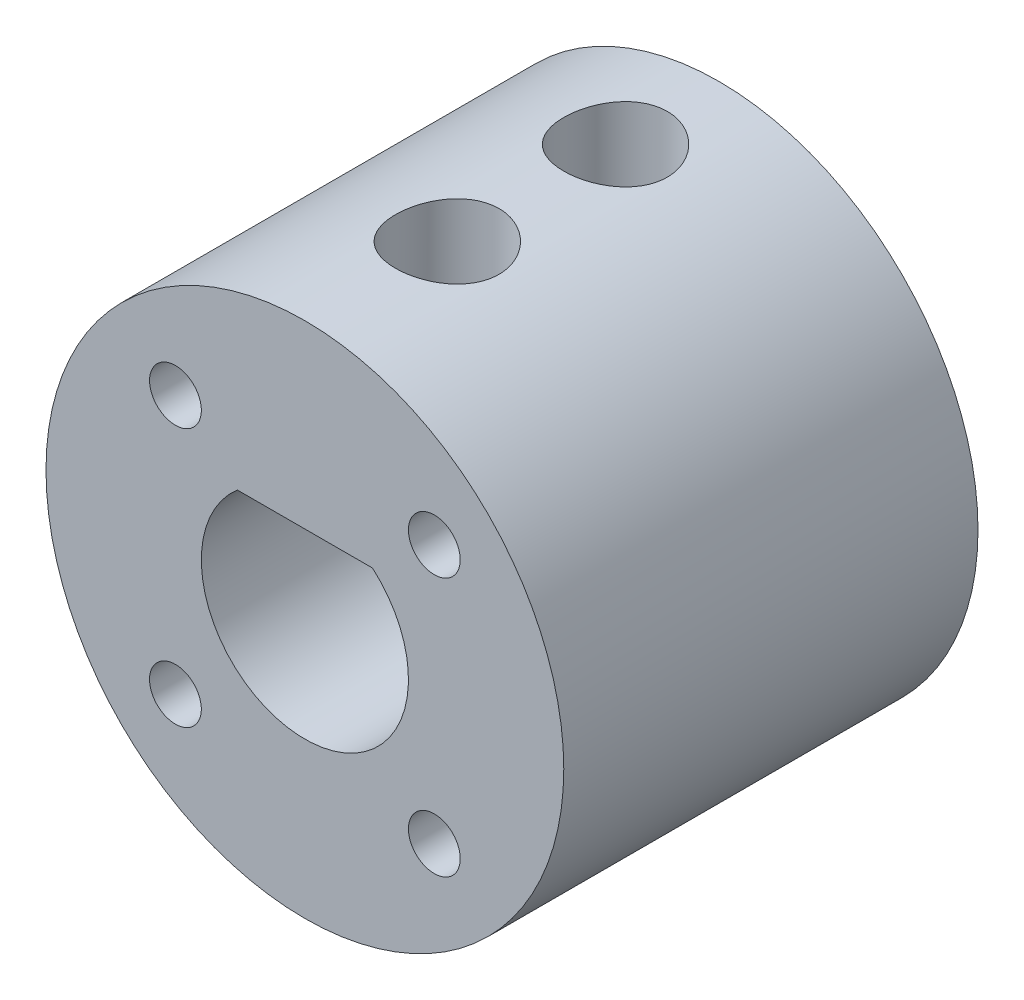
SolidWorks part; units mm, degrees
ref_plane "Alzado" through (0, 0, 0) normal (0, 0, 1) x (1, 0, 0)
ref_plane "Planta" through (0, 0, 0) normal (0, 1, 0) x (1, 0, 0)
ref_plane "Vista lateral" through (0, 0, 0) normal (1, 0, 0) x (0, 0, -1)
sketch "Croquis1" plane through (0, 0, 0) normal (0, 0, 1) x (1, 0, 0)
  line L0 (2.6113, 3.03) -> (-2.6113, 3.03)
  circle A0 centre (0, 0) radius 10
  arc A1 (-2.6113, 3.03) -> (2.6113, 3.03) centre (0, 0) ccw
  dimension "D1" = 8
  dimension "D2" = 20
  dimension "D3" = 3.03
extrude "Saliente-Extruir1" add sketch "Croquis1" along normal blind 16
sketch "Croquis2" plane through (0, 0, 0) normal (0, 1, 0) x (1, 0, 0)
  line L0 (0, 0) -> (0, -14) construction
  circle A0 centre (0, -4) radius 2
  circle A1 centre (0, -10.5) radius 2
  dimension "D2" = 4
  dimension "D1" = 14
  dimension "D3" = 4
  dimension "D4" = 6.5
extrude "Cortar-Extruir1" cut sketch "Croquis2" along normal blind 20
sketch "Croquis3" plane through (0, 0, 0) normal (0, 0, -1) x (-1, 0, 0)
  line L0 (5, -5) -> (-5, 5) construction
  line L1 (-5, -5) -> (5, 5) construction
  line L3 (-3.5, 5) -> (-4.25, 6.299)
  line L4 (-4.25, 6.299) -> (-5.75, 6.299)
  line L5 (-5.75, 6.299) -> (-6.5, 5)
  line L6 (-6.5, 5) -> (-5.75, 3.701)
  line L7 (-5.75, 3.701) -> (-4.25, 3.701)
  line L8 (-4.25, 3.701) -> (-3.5, 5)
  line L9 (6.4995, 5.0386) -> (5.7163, 6.3179)
  line L10 (5.7163, 6.3179) -> (4.2168, 6.2793)
  line L11 (4.2168, 6.2793) -> (3.5005, 4.9614)
  line L12 (3.5005, 4.9614) -> (4.2837, 3.6821)
  line L13 (4.2837, 3.6821) -> (5.7832, 3.7207)
  line L14 (5.7832, 3.7207) -> (6.4995, 5.0386)
  line L15 (6.5, -5.0009) -> (5.7508, -3.7014)
  line L16 (5.7508, -3.7014) -> (4.2508, -3.7005)
  line L17 (4.2508, -3.7005) -> (3.5, -4.9991)
  line L18 (3.5, -4.9991) -> (4.2492, -6.2986)
  line L19 (4.2492, -6.2986) -> (5.7492, -6.2995)
  line L20 (5.7492, -6.2995) -> (6.5, -5.0009)
  line L21 (-3.5002, -4.9752) -> (-4.2716, -3.6887)
  line L22 (-4.2716, -3.6887) -> (-5.7714, -3.7135)
  line L23 (-5.7714, -3.7135) -> (-6.4998, -5.0248)
  line L24 (-6.4998, -5.0248) -> (-5.7284, -6.3113)
  line L25 (-5.7284, -6.3113) -> (-4.2286, -6.2865)
  line L26 (-4.2286, -6.2865) -> (-3.5002, -4.9752)
  line L31 (-5, -5) -> (5, 5) construction
  line L32 (-5, 5) -> (5, -5) construction
  circle A0 centre (-5, 5) radius 1.299 construction
  circle A1 centre (5, 5) radius 1.299 construction
  circle A2 centre (5, -5) radius 1.299 construction
  circle A3 centre (-5, -5) radius 1.299 construction
  point P0 (0, 0)
  point P4 (0, 0)
  point P9 (0, 0)
  dimension "D1" = 90
  dimension "D2" = 1.5
  dimension "D3" = 5
extrude "Cortar-Extruir2" cut sketch "Croquis3" against normal blind 3
sketch "Croquis5" plane through (0, 0, 3) normal (0, 0, -1) x (-1, 0, 0)
  circle A0 centre (-5, 5) radius 1
  circle A1 centre (5, 5) radius 1
  circle A2 centre (5.0008, -4.9991) radius 1
  circle A3 centre (-5, -4.9991) radius 1
  dimension "D1" = 2
  dimension "D2" = 5
extrude "Cortar-Extruir3" cut sketch "Croquis5" against normal through all
